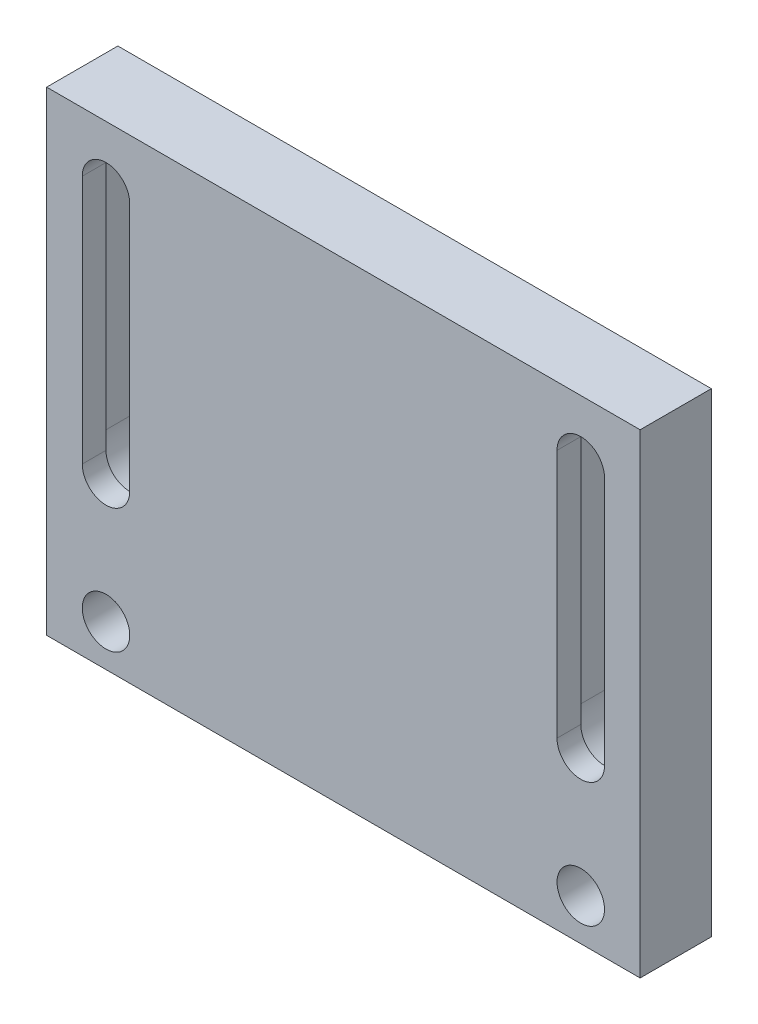
SolidWorks part; units mm, degrees
ref_plane "Front Plane" through (0, 0, 0) normal (0, 0, 1) x (1, 0, 0)
ref_plane "Top Plane" through (0, 0, 0) normal (0, 1, 0) x (1, 0, 0)
ref_plane "Right Plane" through (0, 0, 0) normal (1, 0, 0) x (0, 0, -1)
sketch "Sketch1" plane through (0, 0, 0) normal (0, 0, 1) x (1, 0, 0)
  line L1 (-25, -20) -> (25, -20)
  line L2 (-25, -20) -> (-25, 20)
  line L3 (-25, 20) -> (25, 20)
  line L4 (25, -20) -> (25, 20)
  line L5 (-25, -20) -> (25, 20) construction
  line L6 (-25, 20) -> (25, -20) construction
  point P0 (0, 0)
  dimension "D1" = 50
  dimension "D2" = 40
extrude "Boss-Extrude1" add sketch "Sketch1" along normal blind 6
sketch "Sketch6" plane through (0, 0, 0) normal (0, 0, -1) x (-1, 0, 0)
  line L0 (-16.5, 15) -> (-16.5, -6)
  line L1 (-23.5, 15) -> (-23.5, -6)
  line L6 (23.5, 15) -> (23.5, -6)
  line L7 (16.5, 15) -> (16.5, -6)
  arc A3 (-23.5, -6) -> (-16.5, -6) centre (-20, -6) ccw
  arc A4 (-23.5, 15) -> (-16.5, 15) centre (-20, 15) cw
  arc A5 (23.5, 15) -> (16.5, 15) centre (20, 15) ccw
  arc A6 (23.5, -6) -> (16.5, -6) centre (20, -6) cw
extrude "Cut-Extrude3" cut sketch "Sketch6" against normal blind 4
sketch "Sketch7" plane through (0, 0, 0) normal (0, 0, -1) x (-1, 0, 0)
  line L4 (-22, 15) -> (-22, -6)
  line L5 (-18, 15) -> (-18, -6)
  line L9 (18, 15) -> (18, -6)
  line L10 (22, 15) -> (22, -6)
  arc A6 (-18, 15) -> (-22, 15) centre (-20, 15) ccw
  arc A7 (-22, -6) -> (-18, -6) centre (-20, -6) ccw
  arc A8 (22, -6) -> (18, -6) centre (20, -6) cw
  arc A9 (18, 15) -> (22, 15) centre (20, 15) cw
  circle A12 centre (-20, -16.5) radius 2
  circle A13 centre (20, -16.5) radius 2
extrude "Cut-Extrude4" cut sketch "Sketch7" against normal up to surface (6 mm away) up to face at (0, 0, 6)
